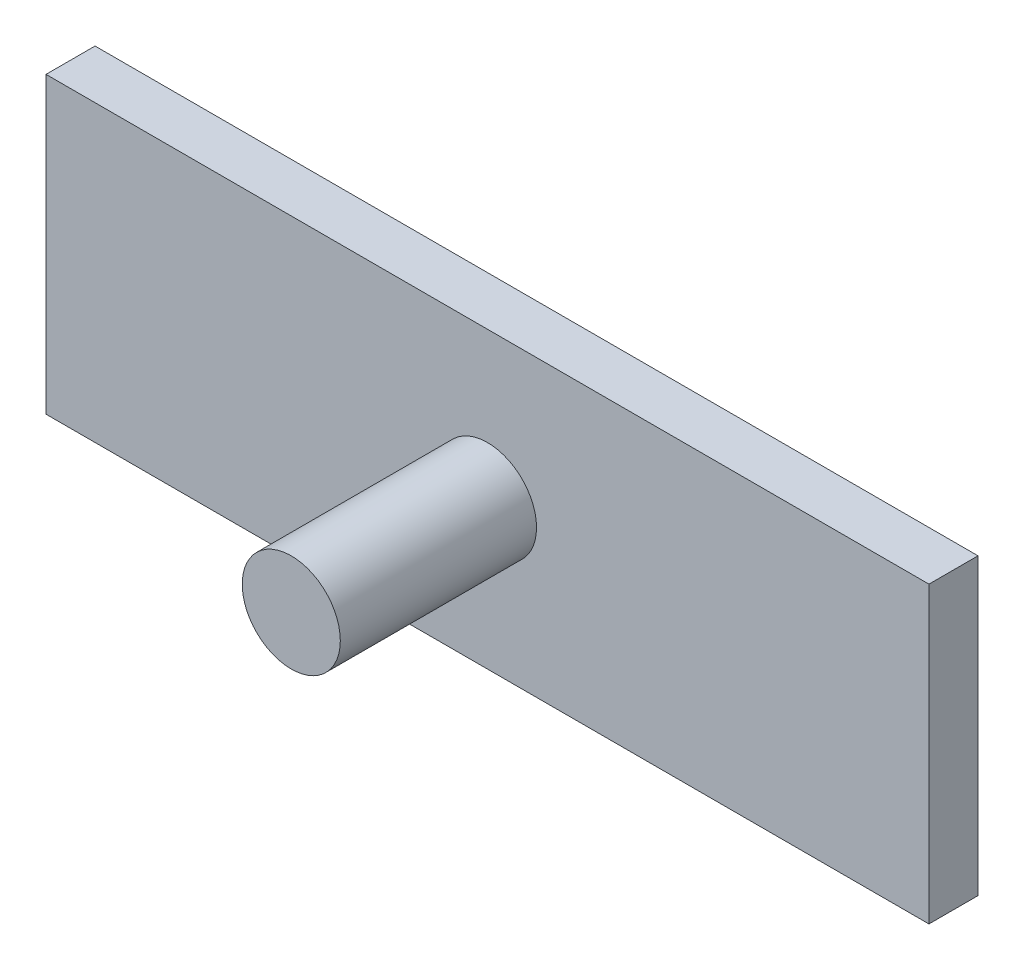
SolidWorks part; units mm, degrees
ref_plane "Plan de face" through (0, 0, 0) normal (0, 0, 1) x (1, 0, 0)
ref_plane "Plan de dessus" through (0, 0, 0) normal (0, 1, 0) x (1, 0, 0)
ref_plane "Plan de droite" through (0, 0, 0) normal (1, 0, 0) x (0, 0, -1)
sketch "Esquisse1" plane through (0, 0, 0) normal (0, 0, 1) x (1, 0, 0)
  line L1 (0, 0) -> (-90, 0)
  line L2 (0, 0) -> (0, 30)
  line L3 (0, 30) -> (-90, 30)
  line L4 (-90, 0) -> (-90, 30)
  dimension "D1" = 90
  dimension "D2" = 30
extrude "Boss.-Extru.1" add sketch "Esquisse1" along normal blind 5
sketch "Esquisse2" plane through (0, 0, 5) normal (0, 0, 1) x (1, 0, 0)
  line L0 (-90, 30) -> (0, 0) construction
  line L1 (-90, 0) -> (0, 30) construction
  circle A0 centre (-45, 15) radius 5
  dimension "D1" = 10
extrude "Boss.-Extru.2" add sketch "Esquisse2" along normal blind 20
sketch "Esquisse3" plane through (0, 0, 25) normal (0, 0, 1) x (1, 0, 0)
  circle A0 centre (-45, 15) radius 8.898
